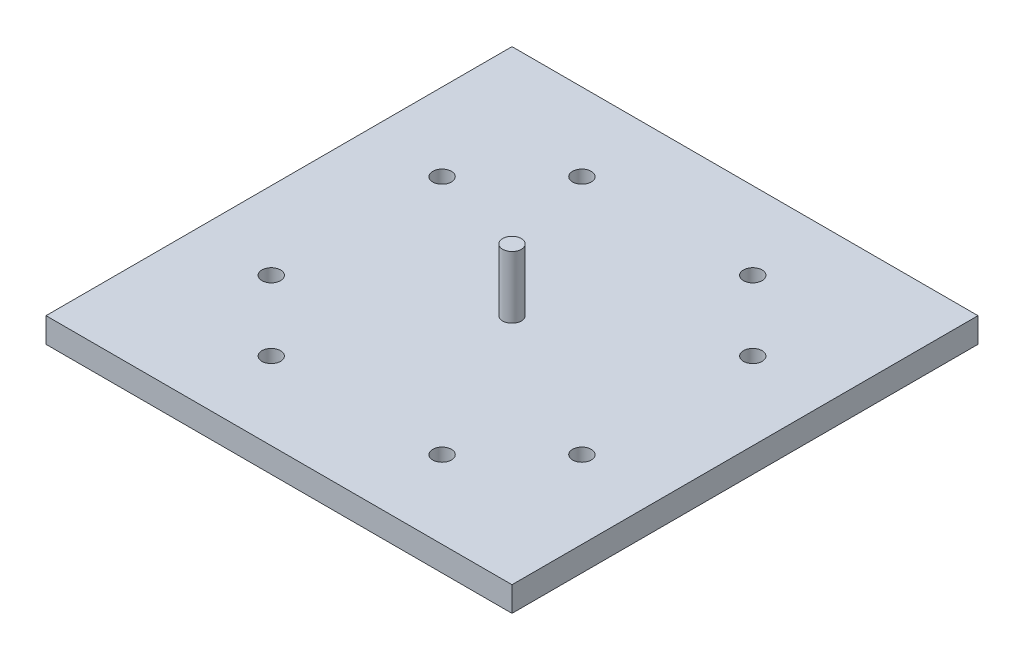
SolidWorks part; units mm, degrees
ref_plane "Front Plane" through (0, 0, 0) normal (0, 0, 1) x (1, 0, 0)
ref_plane "Top Plane" through (0, 0, 0) normal (0, 1, 0) x (1, 0, 0)
ref_plane "Right Plane" through (0, 0, 0) normal (1, 0, 0) x (0, 0, -1)
sketch "Sketch1" plane through (0, 0, 0) normal (0, 1, 0) x (1, 0, 0)
  line L0 (15, 0) -> (15, 30) construction
  line L1 (0, 0) -> (30, 0)
  line L2 (0, 0) -> (0, 30)
  line L3 (0, 30) -> (30, 30)
  line L4 (30, 0) -> (30, 30)
  line L5 (15, 13) -> (19.25, 13)
  dimension "D1" = 30
  dimension "D2" = 30
  dimension "D3" = 4.25
  dimension "D4" = 13
extrude "Boss-Extrude1" add sketch "Sketch1" along normal blind 1.6
sketch "Sketch2" plane through (0, 1.6, 0) normal (0, 1, 0) x (1, 0, 0)
  line L0 (15, 30) -> (15, 0) construction
  line L1 (0, 30) -> (30, 30) construction
  line L2 (0, 0) -> (30, 0) construction
  line L3 (15, 5) -> (20.5, 5) construction
  line L4 (30, 15) -> (0, 15) construction
  line L5 (30, 0) -> (30, 30) construction
  line L6 (0, 0) -> (0, 30) construction
  circle A0 centre (20.5, 5) radius 0.6
  circle A1 centre (9.5, 5) radius 0.6
  circle A2 centre (20.5, 25) radius 0.6
  circle A3 centre (9.5, 25) radius 0.6
  dimension "D3" = 1.2
  dimension "D1" = 5.5
  dimension "D2" = 10
extrude "Cut-Extrude1" cut sketch "Sketch2" against normal blind 1.6
pattern_circular "CirPattern1" count 2 every 90 about axis through (15, 0, -15) along (0, 1, 0) of "Cut-Extrude1"
sketch "Sketch4" plane through (0, 1.6, 0) normal (0, 1, 0) x (1, 0, 0)
  line L0 (0, 15) -> (30, 15) construction
  line L1 (0, 0) -> (0, 30) construction
  line L2 (30, 0) -> (30, 30) construction
  line L3 (15, 0) -> (15, 15) construction
  line L4 (0, 0) -> (30, 0) construction
  circle A0 centre (15, 15) radius 0.6
  dimension "D1" = 1.2
extrude "Boss-Extrude2" add sketch "Sketch4" along normal blind 4
